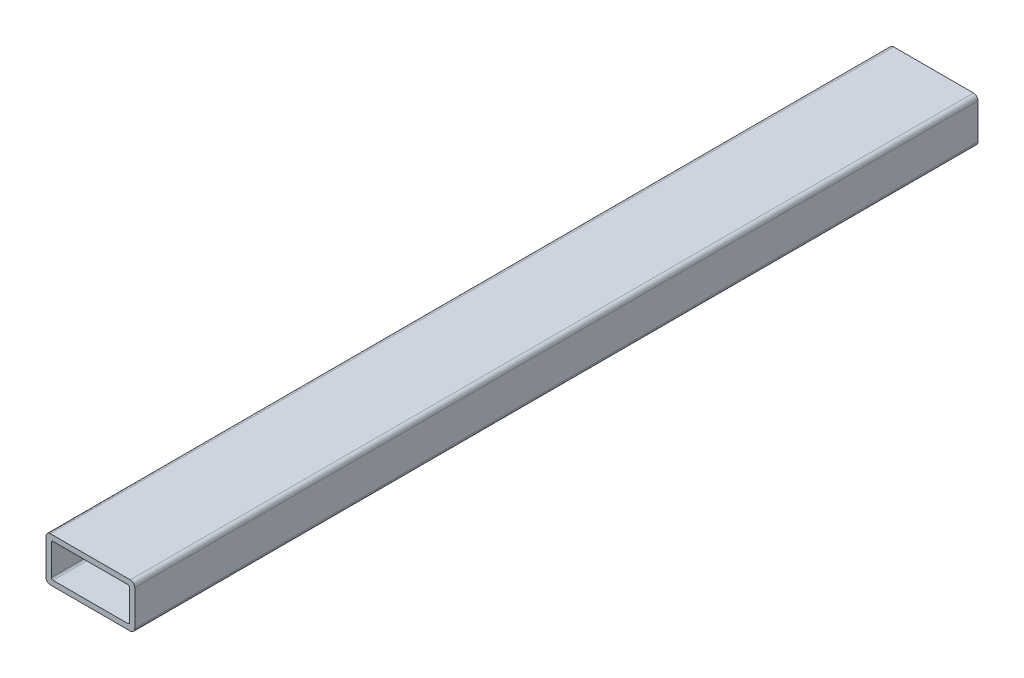
SolidWorks part; units mm, degrees
ref_plane "Front" through (0, 0, 0) normal (0, 0, 1) x (1, 0, 0)
ref_plane "Top" through (0, 0, 0) normal (0, 1, 0) x (1, 0, 0)
ref_plane "Right" through (0, 0, 0) normal (1, 0, 0) x (0, 0, -1)
sketch "Sketch1" plane through (0, 0, 0) normal (0, 0, 1) x (1, 0, 0)
  line L0 (-22.352, 0) -> (-25.4, 0) construction
  line L1 (22.86, -12.7) -> (-22.86, -12.7)
  line L2 (25.4, -10.16) -> (25.4, 10.16)
  line L3 (22.86, 12.7) -> (-22.86, 12.7)
  line L4 (-25.4, -10.16) -> (-25.4, 10.16)
  line L5 (25.4, -12.7) -> (-25.4, 12.7) construction
  line L6 (25.4, 12.7) -> (-25.4, -12.7) construction
  line L7 (21.3868, 9.652) -> (-21.3868, 9.652)
  line L8 (22.352, 8.6868) -> (22.352, -8.6868)
  line L9 (21.3868, -9.652) -> (-21.3868, -9.652)
  line L10 (-22.352, 8.6868) -> (-22.352, -8.6868)
  line L11 (22.352, 9.652) -> (-22.352, -9.652) construction
  line L12 (22.352, -9.652) -> (-22.352, 9.652) construction
  line L13 (0, -9.652) -> (0, -12.7) construction
  line L14 (22.352, -8.6868) -> (22.352, -12.7) construction
  line L16 (22.352, -12.7) -> (25.4, -12.7) construction
  arc A0 (-21.3868, -9.652) -> (-22.352, -8.6868) centre (-21.3868, -8.6868) cw
  arc A1 (22.352, -8.6868) -> (21.3868, -9.652) centre (21.3868, -8.6868) cw
  arc A2 (21.3868, 9.652) -> (22.352, 8.6868) centre (21.3868, 8.6868) cw
  arc A3 (-21.3868, 9.652) -> (-22.352, 8.6868) centre (-21.3868, 8.6868) ccw
  arc A4 (22.86, -12.7) -> (25.4, -10.16) centre (22.86, -10.16) ccw
  arc A5 (25.4, 10.16) -> (22.86, 12.7) centre (22.86, 10.16) ccw
  arc A6 (-22.86, 12.7) -> (-25.4, 10.16) centre (-22.86, 10.16) ccw
  arc A7 (-22.86, -12.7) -> (-25.4, -10.16) centre (-22.86, -10.16) cw
  point P0 (0, 0)
  point P6 (0, 0)
  dimension "D2" = 0.9652
  dimension "D3" = 2.54
sketch "Sketch2" plane through (0, 0, 0) normal (1, 0, 0) x (0, 0, -1)
  line L0 (-152.4, 0) -> (152.4, 0) construction
  dimension "Length" = 304.8
ref_plane "Plane1" through (25.4, 0, 0) normal (1, 0, 0) x (0, 0, -1)
sketch "Sketch5" plane through (25.4, 0, 0) normal (1, 0, 0) x (0, 0, -1)
  line L0 (-152.4, 12.7) -> (-152.4, -12.7) construction
  line L1 (152.4, 12.7) -> (152.4, -12.7) construction
sketch "Sketch4" plane through (0, 0, 0) normal (0, 0, 1) x (1, 0, 0)
  line L0 (25.4, -10.16) -> (25.4, 10.16) construction
  line L1 (22.86, 12.7) -> (-22.86, 12.7) construction
  line L2 (-25.4, -10.16) -> (-25.4, 10.16) construction
  line L3 (22.86, -12.7) -> (-22.86, -12.7) construction
  line L4 (22.352, 8.6868) -> (22.352, -8.6868) construction
  line L5 (21.3868, -9.652) -> (-21.3868, -9.652) construction
  line L6 (-22.352, 8.6868) -> (-22.352, -8.6868) construction
  line L7 (21.3868, 9.652) -> (-21.3868, 9.652) construction
  line L8 (25.4, -10.16) -> (25.4, 10.16)
  line L9 (22.86, 12.7) -> (-22.86, 12.7)
  line L10 (-25.4, -10.16) -> (-25.4, 10.16)
  line L11 (22.86, -12.7) -> (-22.86, -12.7)
  line L12 (22.352, 8.6868) -> (22.352, -8.6868)
  line L13 (21.3868, -9.652) -> (-21.3868, -9.652)
  line L14 (-22.352, 8.6868) -> (-22.352, -8.6868)
  line L15 (21.3868, 9.652) -> (-21.3868, 9.652)
  arc A0 (25.4, 10.16) -> (22.86, 12.7) centre (22.86, 10.16) ccw construction
  arc A1 (-22.86, 12.7) -> (-25.4, 10.16) centre (-22.86, 10.16) ccw construction
  arc A2 (-25.4, -10.16) -> (-22.86, -12.7) centre (-22.86, -10.16) ccw construction
  arc A3 (22.86, -12.7) -> (25.4, -10.16) centre (22.86, -10.16) ccw construction
  arc A4 (21.3868, -9.652) -> (22.352, -8.6868) centre (21.3868, -8.6868) ccw construction
  arc A5 (-22.352, -8.6868) -> (-21.3868, -9.652) centre (-21.3868, -8.6868) ccw construction
  arc A6 (-21.3868, 9.652) -> (-22.352, 8.6868) centre (-21.3868, 8.6868) ccw construction
  arc A7 (22.352, 8.6868) -> (21.3868, 9.652) centre (21.3868, 8.6868) ccw construction
  arc A8 (25.4, 10.16) -> (22.86, 12.7) centre (22.86, 10.16) ccw
  arc A9 (-22.86, 12.7) -> (-25.4, 10.16) centre (-22.86, 10.16) ccw
  arc A10 (-25.4, -10.16) -> (-22.86, -12.7) centre (-22.86, -10.16) ccw
  arc A11 (22.86, -12.7) -> (25.4, -10.16) centre (22.86, -10.16) ccw
  arc A12 (21.3868, -9.652) -> (22.352, -8.6868) centre (21.3868, -8.6868) ccw
  arc A13 (-22.352, -8.6868) -> (-21.3868, -9.652) centre (-21.3868, -8.6868) ccw
  arc A14 (-21.3868, 9.652) -> (-22.352, 8.6868) centre (-21.3868, 8.6868) ccw
  arc A15 (22.352, 8.6868) -> (21.3868, 9.652) centre (21.3868, 8.6868) ccw
extrude "Boss-Extrude1" add sketch "Sketch4" along normal blind 482.6
sketch "Sketch6" plane through (0, 12.7, 0) normal (0, 1, 0) x (1, 0, 0)
  line L0 (0, -482.6) -> (0, -311.15) construction
  line L2 (-22.86, -311.15) -> (22.86, -311.15) construction
  line L3 (-22.86, 0) -> (-22.86, -482.6) construction
  line L4 (22.86, 0) -> (22.86, -482.6) construction
  line L5 (-22.86, -171.45) -> (22.86, -171.45) construction
  line L6 (22.86, -482.6) -> (-22.86, -482.6) construction
  line L7 (0, -311.15) -> (0, -171.45) construction
  line L8 (0, -171.45) -> (0, 0) construction
  line L9 (22.86, 0) -> (-22.86, 0) construction
  dimension "D1" = 139.7
equation "\"D3@Sketch1\"=\"Outside Width@Sketch1\"*.05"
equation "\"D2@Sketch1\"=\"D1@Sketch1\"*.05"
